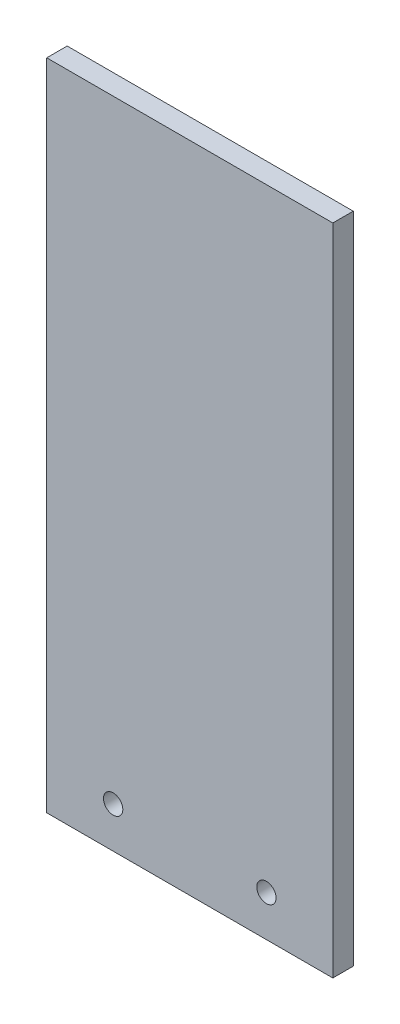
SolidWorks part; units mm, degrees
ref_plane "Front Plane" through (0, 0, 0) normal (0, 0, 1) x (1, 0, 0)
ref_plane "Top Plane" through (0, 0, 0) normal (0, 1, 0) x (1, 0, 0)
ref_plane "Right Plane" through (0, 0, 0) normal (1, 0, 0) x (0, 0, -1)
sketch "Sketch1" plane through (0, 0, 0) normal (0, 1, 0) x (1, 0, 0)
  line L1 (0, 0) -> (88.9, 0)
  line L2 (0, 0) -> (0, 6.35)
  line L3 (0, 6.35) -> (88.9, 6.35)
  line L4 (88.9, 0) -> (88.9, 6.35)
  dimension "D1" = 88.9
  dimension "D2" = 6.35
extrude "Boss-Extrude1" add sketch "Sketch1" along normal blind 203.2
ref_plane "Plane1" through (44.45, 0, 0) normal (-1, 0, 0) x (0, 0, 1)
hole_wizard "Ø6.0 (6) Diameter Hole1" positions "Sketch3" profile "Sketch4" hole size "Ø6.0" standard "ANSI Metric" end condition up to next
sketch "Sketch3" plane through (0, 0, -6.35) normal (0, 0, -1) x (-1, 0, 0)
  line L0 (-20.6375, 12.7) -> (-68.2625, 12.7) construction
  line L2 (-44.45, -3.4925) -> (-44.45, 3.4925) construction
  line L3 (-88.9, 0) -> (0, 0) construction
  point P0 (-20.6375, 12.7)
  point P2 (-68.2625, 12.7)
  point P9 (-44.45, 12.7)
  dimension "D1" = 47.625
  dimension "D2" = 12.7
sketch "Sketch4" plane through (20.6375, 12.7, -6.35) normal (1, 0, 0) x (0, 1, 0)
  line L0 (0, 0) -> (0, 6.35)
  line L1 (0, 6.35) -> (3, 6.35)
  line L2 (3, 6.35) -> (3, 0)
  line L5 (3, 0) -> (0, 0)
  line L11 (0, -6.35) -> (0, 107.95) construction
  dimension "Thru Hole Dia." = 6
  dimension "Thru Hole Depth" = 6.35
